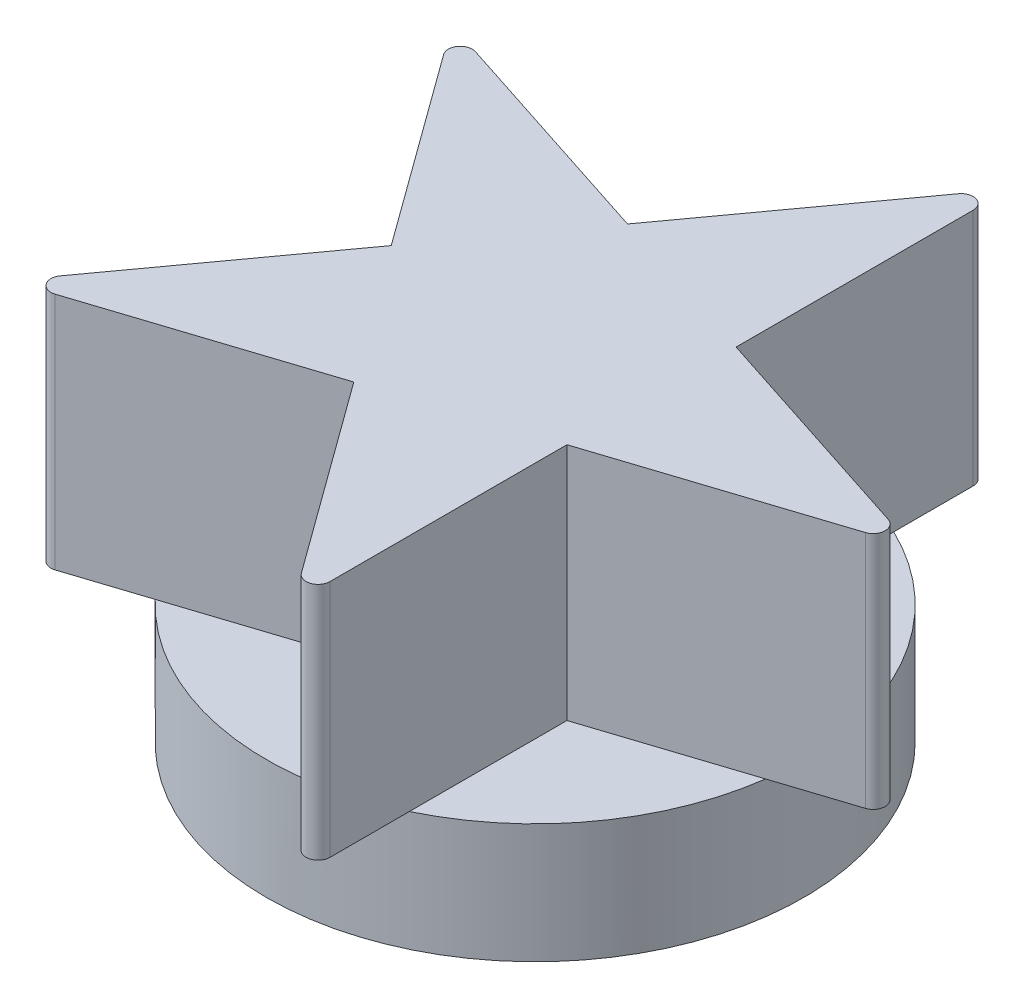
SolidWorks part; units mm, degrees
ref_plane "Front Plane" through (0, 0, 0) normal (0, 0, 1) x (1, 0, 0)
ref_plane "Top Plane" through (0, 0, 0) normal (0, 1, 0) x (1, 0, 0)
ref_plane "Right Plane" through (0, 0, 0) normal (1, 0, 0) x (0, 0, -1)
sketch "Sketch1" plane through (0, 0, 0) normal (0, 1, 0) x (1, 0, 0)
  circle A0 centre (0, 0) radius 22.5
  dimension "D1" = 45
extrude "Boss-Extrude1" add sketch "Sketch1" along normal blind 10
sketch "Sketch2" plane through (0, 10, 0) normal (0, 1, 0) x (1, 0, 0)
  line L5 (9.7476, 26.9223) -> (9.7476, 7.082)
  line L6 (28.6168, -0.9511) -> (9.7476, -7.082)
  line L7 (-23.7105, 16.0511) -> (-12.0487, 0)
  line L8 (-23.7105, -16.0511) -> (-12.0487, 0)
  line L9 (28.6168, 0.9511) -> (9.7476, 7.082)
  line L10 (-3.7232, 11.459) -> (7.9386, 27.5101)
  line L11 (-3.7232, 11.459) -> (-22.5925, 17.59)
  line L12 (9.7476, -7.082) -> (9.7476, -26.9223)
  line L13 (-3.7232, -11.459) -> (-22.5925, -17.59)
  line L14 (-3.7232, -11.459) -> (7.9386, -27.5101)
  arc A0 (9.7476, -26.9223) -> (7.9386, -27.5101) centre (8.7476, -26.9223) cw
  arc A1 (28.6168, 0.9511) -> (28.6168, -0.9511) centre (28.3078, 0) cw
  arc A2 (9.7476, 26.9223) -> (7.9386, 27.5101) centre (8.7476, 26.9223) ccw
  arc A3 (-22.5925, 17.59) -> (-23.7105, 16.0511) centre (-22.9015, 16.6389) ccw
  arc A4 (-22.5925, -17.59) -> (-23.7105, -16.0511) centre (-22.9015, -16.6389) cw
  point P14 (31.5439, 0)
  point P19 (-25.5195, 18.541)
  dimension "D1" = 60
  dimension "D2" = 1
extrude "Boss-Extrude2" add sketch "Sketch2" along normal blind 20
sketch "Sketch3" plane through (0, 0, 0) normal (0, -1, 0) x (1, 0, 0)
  line L0 (14.5514, 2.7786) -> (0, 30)
  line L1 (0, 30) -> (-14.5514, 2.7786)
  circle A0 centre (0, -5) radius 16.5
  circle A2 centre (0, 0) radius 22.5 construction
  circle A4 centre (0, 0) radius 21.5
  circle A5 centre (0, 0) radius 21.5
  dimension "D1" = 33
  dimension "D2" = 35
  dimension "D3" = 5
  dimension "D4" = 1
extrude "Cut-Extrude2" cut sketch "Sketch3" against normal blind 5 contours L0 A5 L1 A0 | A0
